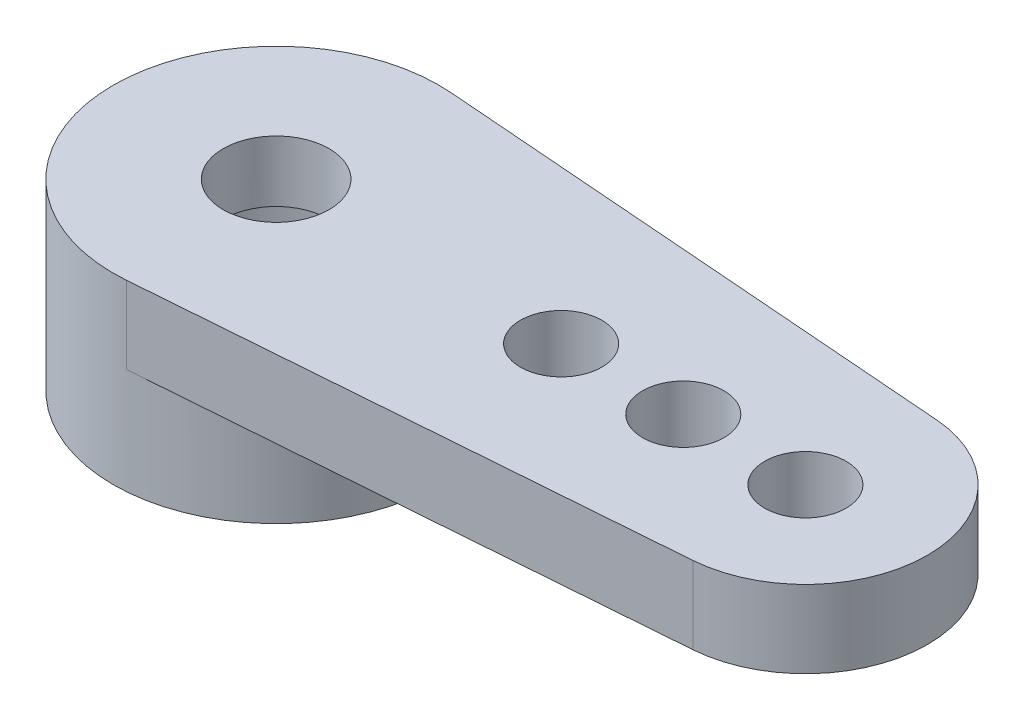
SolidWorks part; units mm, degrees
material "普通碳钢"
ref_plane "前视基准面" through (0, 0, 0) normal (0, 0, 1) x (1, 0, 0)
ref_plane "上视基准面" through (0, 0, 0) normal (0, 1, 0) x (1, 0, 0)
ref_plane "右视基准面" through (0, 0, 0) normal (1, 0, 0) x (0, 0, -1)
other "Configuration Table"
sketch "草图1" plane through (0, 0, 0) normal (0, 1, 0) x (1, 0, 0)
  circle A0 centre (0, 0) radius 4
  circle A1 centre (0, 0) radius 1.3
  dimension "D1" = 8
  dimension "D2" = 2.6
extrude "凸台-拉伸1" add sketch "草图1" along normal blind 4.5
sketch "草图2" plane through (0, 4.5, 0) normal (0, 1, 0) x (1, 0, 0)
  line L0 (0, 0) -> (13, 0) construction
  line L1 (0.3077, 3.9881) -> (13.2308, 2.9911)
  line L2 (0.3077, -3.9881) -> (13.2308, -2.9911)
  circle A0 centre (13, 0) radius 1
  circle A1 centre (10, 0) radius 1
  circle A2 centre (7, 0) radius 1
  circle A3 centre (13, 0) radius 3
  circle A4 centre (0, 0) radius 4 construction
  circle A5 centre (0, 0) radius 4
  point P9 (16, 0)
  dimension "D1" = 2
  dimension "D2" = 2
  dimension "D3" = 2
  dimension "D4" = 7
  dimension "D5" = 3
  dimension "D6" = 3
  dimension "D7" = 16
extrude "凸台-拉伸2" add sketch "草图2" against normal blind 1.9
sketch "草图3" plane through (0, 0, 0) normal (0, -1, 0) x (1, 0, 0)
  circle A0 centre (0, 0) radius 3
  dimension "D1" = 6
extrude "切除-拉伸1" cut sketch "草图3" against normal blind 3
